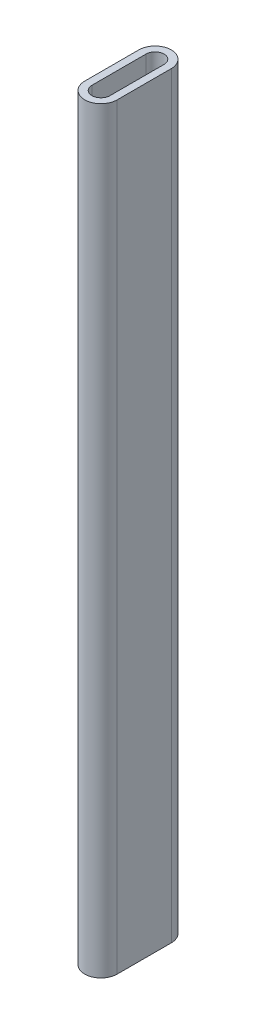
SolidWorks part; units mm, degrees
material "3.0505 (EN-AW 3105)"
ref_plane "Front" through (0, 0, 0) normal (0, 0, 1) x (1, 0, 0)
ref_plane "Top" through (0, 0, 0) normal (0, 1, 0) x (1, 0, 0)
ref_plane "Right" through (0, 0, 0) normal (1, 0, 0) x (0, 0, -1)
sketch "Sketch2" plane through (0, 0, 0) normal (0, 1, 0) x (1, 0, 0)
  line L44 (-4.5984, 8.0213) -> (-4.5984, -6.9787)
  line L45 (4.4016, 8.0213) -> (4.4016, -6.9787)
  line L47 (-2.5984, 8.0213) -> (-2.5984, -6.9787)
  line L48 (2.4016, 8.0213) -> (2.4016, -6.9787)
  arc A0 (2.4016, 8.0213) -> (-2.5984, 8.0213) centre (-0.0984, 8.0213) ccw
  arc A1 (-2.5984, -6.9787) -> (2.4016, -6.9787) centre (-0.0984, -6.9787) ccw
  arc A4 (4.4016, 8.0213) -> (-4.5984, 8.0213) centre (-0.0984, 8.0213) ccw
  arc A5 (-4.5984, -6.9787) -> (4.4016, -6.9787) centre (-0.0984, -6.9787) ccw
  dimension "D1" = 5
  dimension "D2" = 2
  dimension "D3" = 2
  dimension "D4" = 9
extrude "Boss-Extrude1" add sketch "Sketch2" along normal blind 210
